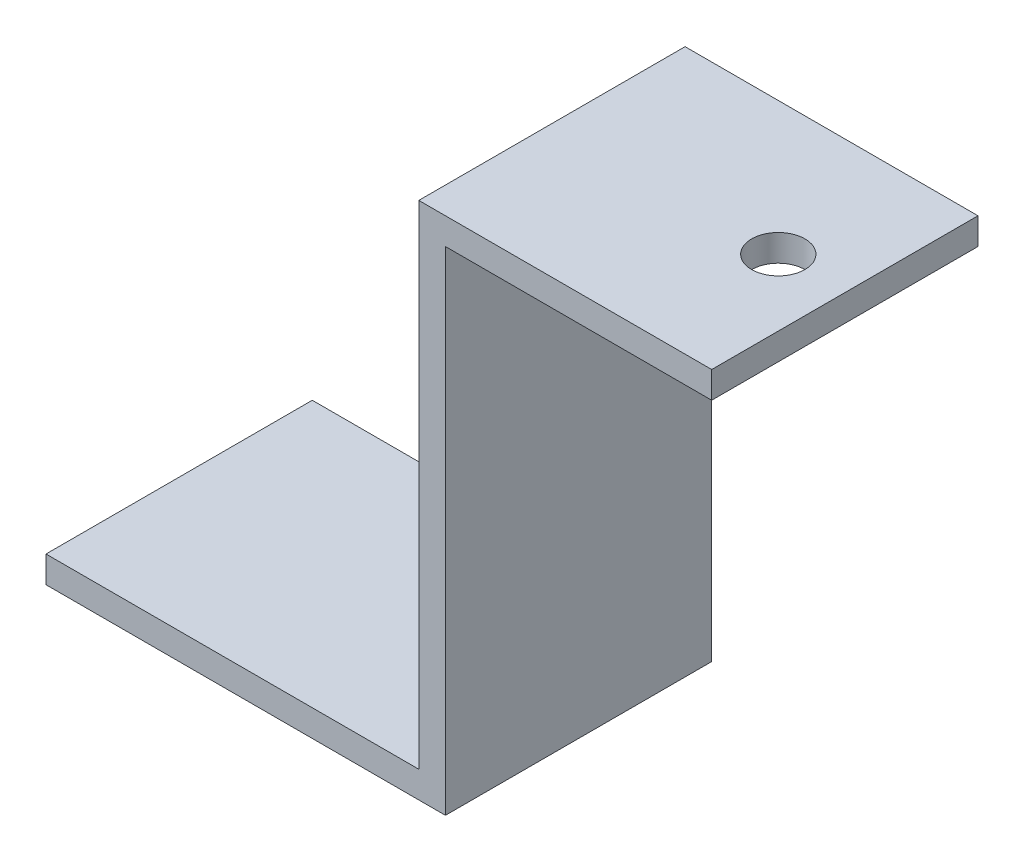
SolidWorks part; units mm, degrees
ref_plane "前视基准面" through (0, 0, 0) normal (0, 0, 1) x (1, 0, 0)
ref_plane "上视基准面" through (0, 0, 0) normal (0, 1, 0) x (1, 0, 0)
ref_plane "右视基准面" through (0, 0, 0) normal (1, 0, 0) x (0, 0, -1)
sketch "草图1" plane through (0, 0, 0) normal (0, 0, 1) x (1, 0, 0)
  line L0 (-17.1756, 36.3603) -> (-7.1756, 36.3603)
  line L1 (-7.1756, 36.3603) -> (2.8244, 36.3603)
  line L2 (2.8244, 36.3603) -> (2.8244, 34.3603)
  line L3 (2.8244, 34.3603) -> (-17.1756, 34.3603)
  line L4 (-17.1756, 34.3603) -> (-17.1756, -0.6397)
  line L5 (-17.1756, -0.6397) -> (-17.1756, -2.6397)
  line L6 (-17.1756, -2.6397) -> (-47.1756, -2.6397)
  line L7 (-47.1756, -2.6397) -> (-47.1756, -0.6397)
  line L8 (-47.1756, -0.6397) -> (-19.1756, -0.6397)
  line L9 (-19.1756, -0.6397) -> (-19.1756, 36.3603)
  line L10 (-19.1756, 36.3603) -> (-17.1756, 36.3603)
  dimension "D7" = 2
  dimension "D1" = 10
  dimension "D2" = 10
  dimension "D3" = 2
  dimension "D4" = 35
  dimension "D5" = 2
  dimension "D6" = 30
  dimension "D8" = 28
extrude "凸台-拉伸1" add sketch "草图1" along normal blind 20
sketch "草图2" plane through (0, 36.3603, 0) normal (0, 1, 0) x (1, 0, 0)
  line L0 (2.8244, -10) -> (-2.1756, -10) construction
  line L1 (2.8244, -20) -> (2.8244, 0) construction
  circle A0 centre (-2.1756, -10) radius 2
  dimension "D2" = 4
  dimension "D1" = 5
extrude "切除-拉伸1" cut sketch "草图2" against normal blind 20
